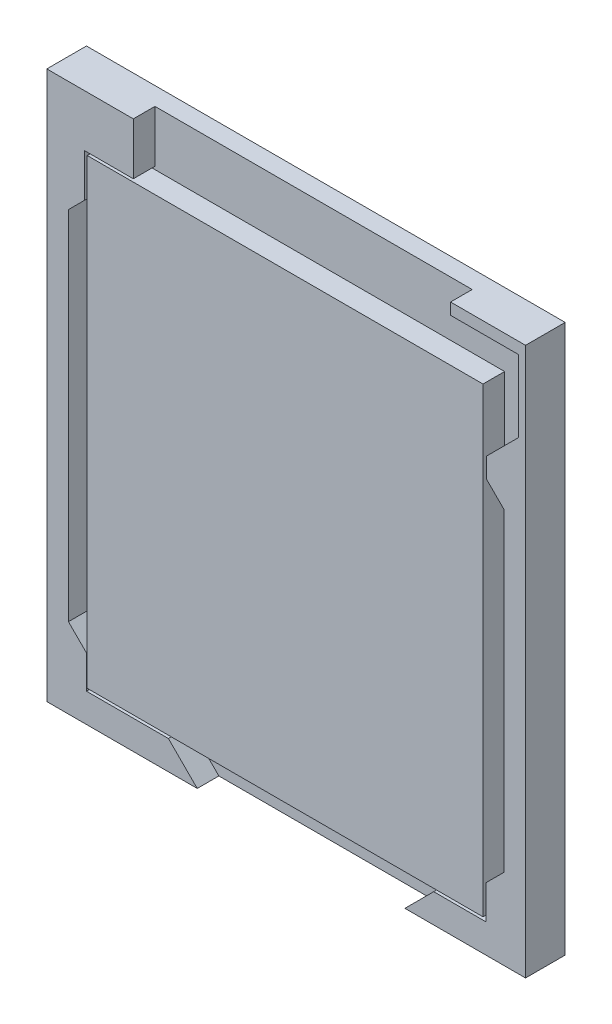
SolidWorks part; units mm, degrees
material "Nylon 101"
ref_plane "Front Plane" through (0, 0, 0) normal (0, 0, 1) x (1, 0, 0)
ref_plane "Top Plane" through (0, 0, 0) normal (0, 1, 0) x (1, 0, 0)
ref_plane "Right Plane" through (0, 0, 0) normal (1, 0, 0) x (0, 0, -1)
sketch "Sketch1" plane through (0, 0, 0) normal (0, 0, 1) x (1, 0, 0)
  line L1 (-16.6, -19) -> (16.6, -19)
  line L2 (-16.6, -19) -> (-16.6, 19)
  line L3 (-16.6, 19) -> (16.6, 19)
  line L4 (16.6, -19) -> (16.6, 19)
  line L5 (-16.6, -19) -> (16.6, 19) construction
  line L6 (-16.6, 19) -> (16.6, -19) construction
  point P0 (0, 0)
  dimension "D1" = 33.2
  dimension "D2" = 38
extrude "Boss-Extrude1" add sketch "Sketch1" along normal blind 2.75
sketch "Sketch2" plane through (0, 0, 2.75) normal (0, 0, 1) x (1, 0, 0)
  line L0 (-6.1677, -19) -> (8.2323, -19)
  line L1 (-16.6, -19) -> (16.6, -19) construction
  line L2 (8.2323, -19) -> (10.2323, -17)
  line L3 (10.2323, -17) -> (13.85, -17)
  line L4 (13.85, -17) -> (13.85, -14.6554)
  line L5 (13.85, -14.6554) -> (15.1, -13.4054)
  line L6 (15.1, -13.4054) -> (15.1, 8.4)
  line L7 (15.1, 8.4) -> (13.9, 9.6)
  line L8 (13.9, 9.6) -> (13.9, 11)
  line L9 (13.9, 11) -> (16.1, 13.2)
  line L10 (16.1, 13.2) -> (16.1, 18.2)
  line L11 (16.1, 18.2) -> (11.4, 18.2)
  line L12 (11.4, 18.2) -> (11.4, 19)
  line L13 (16.6, 19) -> (-16.6, 19) construction
  line L14 (11.4, 19) -> (-10.6, 19)
  line L15 (-10.6, 19) -> (-10.6, 15.4)
  line L16 (-10.6, 15.4) -> (-14, 15.4)
  line L17 (-14, 15.4) -> (-14, 12.4)
  line L18 (-14, 12.4) -> (-15.1, 11.3)
  line L19 (-15.1, 11.3) -> (-15.1, -13.45)
  line L20 (-15.1, -13.45) -> (-13.85, -14.7)
  line L21 (-13.85, -14.7) -> (-13.85, -17)
  line L22 (-13.85, -17) -> (-8.1677, -17)
  line L23 (-8.1677, -17) -> (-6.1677, -19)
  line L24 (16.6, -19) -> (16.6, 19) construction
  line L25 (-16.6, 19) -> (-16.6, -19) construction
  dimension "D1" = 22
  dimension "D2" = 0.8
  dimension "D3" = 0.5
  dimension "D4" = 2.7
  dimension "D5" = 1.4
  dimension "D6" = 1.5
  dimension "D7" = 45
  dimension "D8" = 2
  dimension "D9" = 2.75
  dimension "D10" = 45
  dimension "D11" = 14.4
  dimension "D12" = 1.5
  dimension "D13" = 2
  dimension "D14" = 2.3
  dimension "D15" = 45
  dimension "D16" = 2.75
  dimension "D17" = 24.75
  dimension "D18" = 3
  dimension "D19" = 3.6
  dimension "D20" = 6
  dimension "D21" = 5
extrude "Cut-Extrude1" cut sketch "Sketch2" against normal blind 1.5
sketch "Sketch3" plane through (0, 0, 1.25) normal (0, 0, 1) x (1, 0, 0)
  line L0 (-14, 15.4) -> (-14, 12.4) construction
  line L1 (-13.8, 15.2) -> (13.65, 15.2)
  line L2 (-13.8, 15.2) -> (-13.8, -16.8)
  line L3 (-13.8, -16.8) -> (13.65, -16.8)
  line L4 (13.65, 15.2) -> (13.65, -16.8)
  line L5 (-10.6, 15.4) -> (-14, 15.4) construction
  line L6 (-13.85, -17) -> (-8.1677, -17) construction
  line L7 (13.85, -17) -> (13.85, -14.6554) construction
  dimension "D1" = 0.2
  dimension "D2" = 0.2
  dimension "D3" = 0.2
  dimension "D4" = 0.2
extrude "Boss-Extrude2" add sketch "Sketch3" along normal blind 1.5
